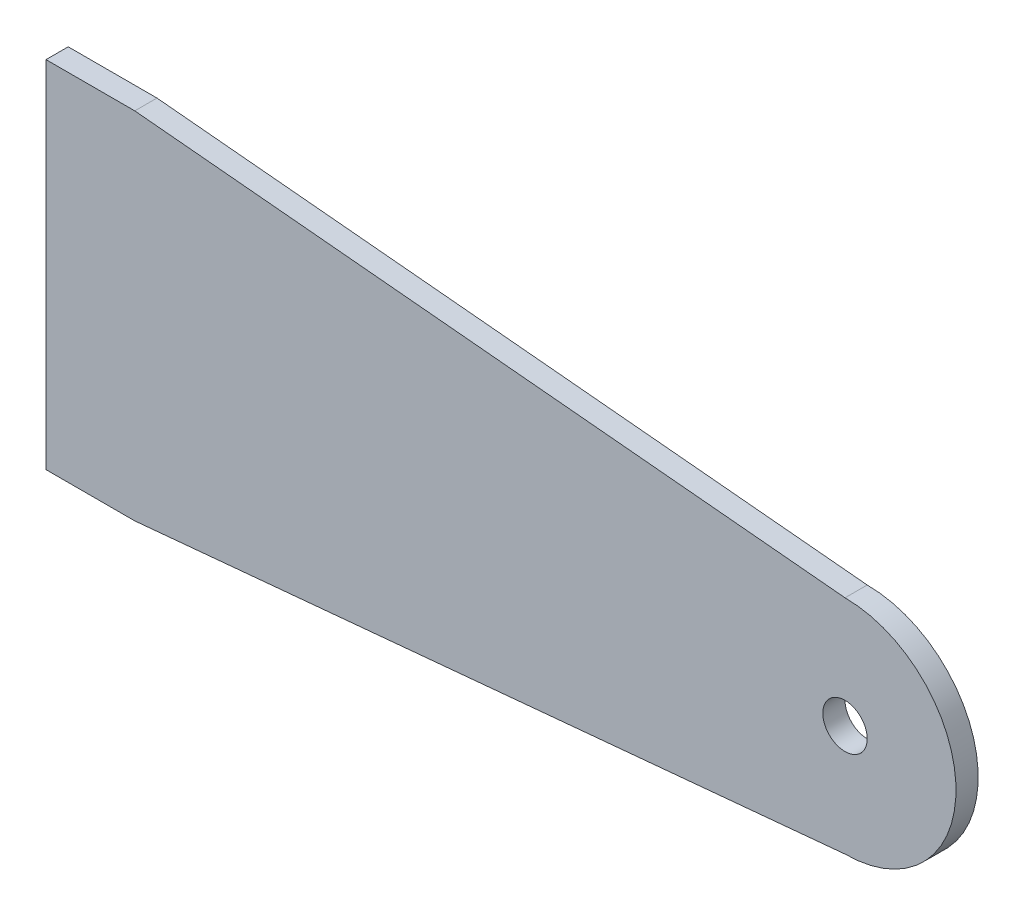
SolidWorks part; units mm, degrees
material "6061-T6 (SS)"
ref_plane "Front Plane" through (0, 0, 0) normal (0, 0, 1) x (1, 0, 0)
ref_plane "Top Plane" through (0, 0, 0) normal (0, 1, 0) x (1, 0, 0)
ref_plane "Right Plane" through (0, 0, 0) normal (1, 0, 0) x (0, 0, -1)
ref_plane "Plane1" through (0, 0, 50.8) normal (0, 0, 1) x (1, 0, 0)
sketch "Sketch1" plane through (0, 0, 50.8) normal (0, 0, 1) x (1, 0, 0)
  line L1 (0, 0) -> (101.6, 0) construction
  line L2 (101.6, 15.875) -> (0, 25.4)
  line L3 (101.6, -15.875) -> (0, -25.4)
  line L4 (101.6, 15.875) -> (101.6, -15.875) construction
  line L5 (0, 25.4) -> (-12.7, 25.4)
  line L6 (-12.7, 25.4) -> (-12.7, -25.4)
  line L7 (-12.7, -25.4) -> (0, -25.4)
  circle A0 centre (101.6, 0) radius 3.175
  arc A1 (101.6, -15.875) -> (101.6, 15.875) centre (101.6, 0) ccw
  point P1 (-12.7, 0)
  point P4 (0, 0)
  dimension "D3" = 6.35
  dimension "D4" = 15.875
  dimension "D1" = 50.8
  dimension "D2" = 101.6
  dimension "D5" = 12.7
  dimension "D6" = 12.7
extrude "Boss-Extrude1" add sketch "Sketch1" along normal blind 3.175
sketch "Sketch2" plane through (0, 0, 0) normal (0, 0, 1) x (1, 0, 0)
  line L0 (0, 25.4) -> (0, -25.4) construction
  point P3 (0, 0)
  dimension "D1" = 50.8
equation "\"HeightOfTubing\"=2"
equation "\"D1@Sketch1\"=\"HeightOfTubing\""
equation "\"D1@Sketch2\"=\"HeightOfTubing\""
